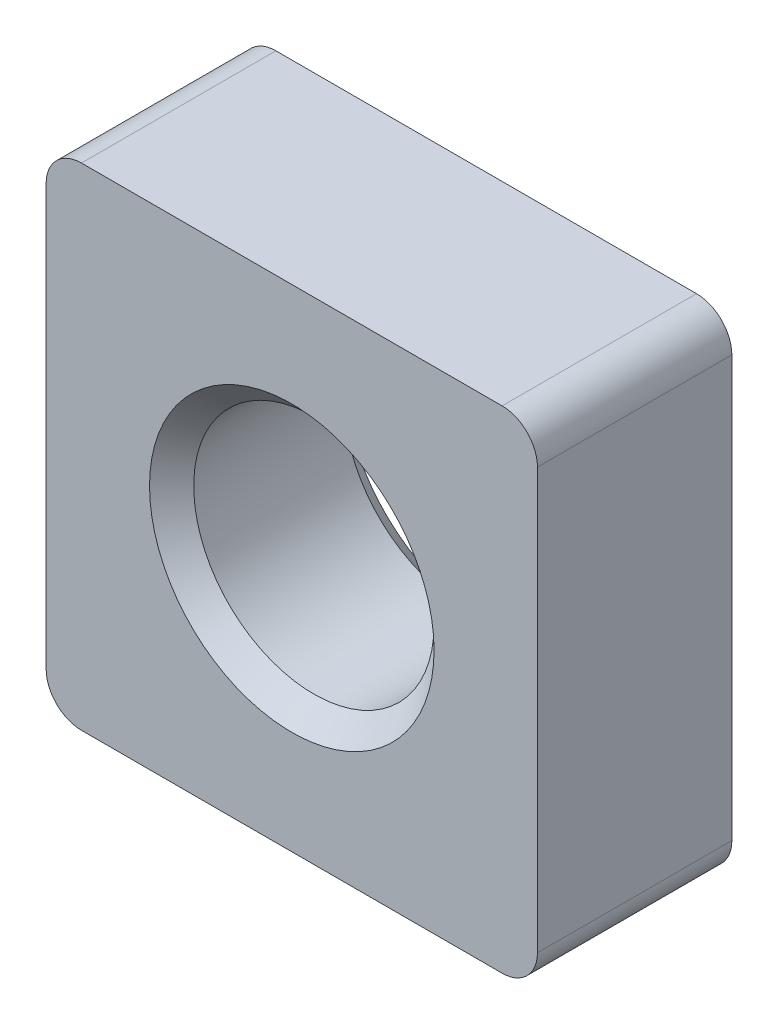
SolidWorks part; units mm, degrees
ref_plane "Спереди" through (0, 0, 0) normal (0, 0, 1) x (1, 0, 0)
ref_plane "Сверху" through (0, 0, 0) normal (0, 1, 0) x (1, 0, 0)
ref_plane "Справа" through (0, 0, 0) normal (1, 0, 0) x (0, 0, -1)
sketch "Эскиз1" plane through (0, 0, 0) normal (0, 0, 1) x (1, 0, 0)
  line L1 (-6.95, -6.95) -> (6.95, -6.95)
  line L2 (-6.95, -6.95) -> (-6.95, 6.95)
  line L3 (-6.95, 6.95) -> (6.95, 6.95)
  line L4 (6.95, -6.95) -> (6.95, 6.95)
  line L5 (-6.95, -6.95) -> (6.95, 6.95) construction
  line L6 (-6.95, 6.95) -> (6.95, -6.95) construction
  point P0 (0, 0)
  dimension "D1" = 13.9
extrude "Бобышка-Вытянуть1" add sketch "Эскиз1" along normal blind 5.5
hole_wizard "Отверстие обработанное метчиком M81" positions "Эскиз2" profile "Эскиз3" tap size "M8" standard "ISO" end condition through all
sketch "Эскиз2" plane through (0, 0, 5.5) normal (0, 0, 1) x (1, 0, 0)
  point P0 (0, 0)
sketch "Эскиз3" plane through (0, 0, 5.5) normal (1, 0, 0) x (0, -1, 0)
  line L0 (0, 0) -> (0, 5.5)
  line L1 (0, 5.5) -> (4.025, 5.5)
  line L2 (3.4, 4.875) -> (3.4, 0.625)
  line L3 (3.4, 0.625) -> (4.025, 0)
  line L5 (4.025, 0) -> (0, 0)
  line L6 (-3.4, 0.625) -> (-4.025, 0) construction
  line L7 (4.025, 5.5) -> (3.4, 4.875)
  line L8 (-4.025, 5.5) -> (-3.4, 4.875) construction
  line L11 (0, -6.35) -> (0, 107.95) construction
  dimension "Диаметр проходного сверла" = 6.8
  dimension "Глубина проходного сверла" = 5.5
  dimension "Диаметр передней зенковки" = 8.05
  dimension "Угол передней зенковки" = 90
  dimension "Диаметр задней зенковки" = 8.05
  dimension "Угол задней зенковки" = 90
cosmetic thread "Отверстие резьбы1" parameters "D2"=8
fillet "Скругление1" radius 1 4 edges at (6.95, 6.95, 2.75) (-6.95, 6.95, 2.75) (6.95, -6.95, 2.75) (-6.95, -6.95, 2.75)
